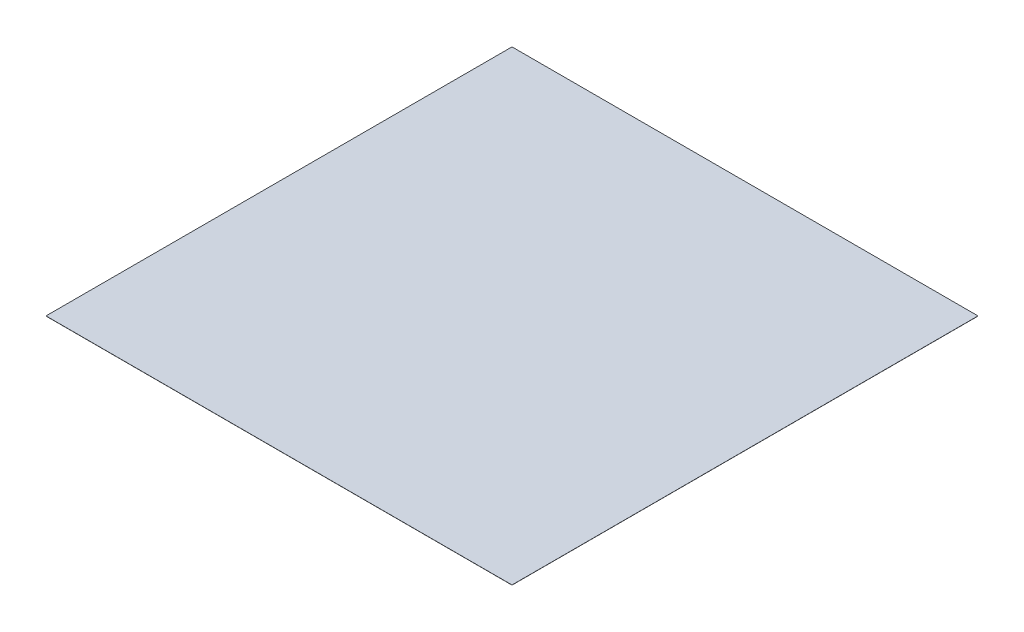
SolidWorks part; units mm, degrees
ref_plane "Front Plane" through (0, 0, 0) normal (0, 0, 1) x (1, 0, 0)
ref_plane "Top Plane" through (0, 0, 0) normal (0, 1, 0) x (1, 0, 0)
ref_plane "Right Plane" through (0, 0, 0) normal (1, 0, 0) x (0, 0, -1)
sketch "Sketch1" plane through (0, 0, 0) normal (0, 1, 0) x (1, 0, 0)
  line L1 (-1423.3391, 980.5341) -> (1576.6609, 980.5341)
  line L2 (-1423.3391, 980.5341) -> (-1423.3391, -2019.4659)
  line L3 (-1423.3391, -2019.4659) -> (1576.6609, -2019.4659)
  line L4 (1576.6609, 980.5341) -> (1576.6609, -2019.4659)
  dimension "D1" = 3000
  dimension "D2" = 3000
extrude "Boss-Extrude1" add sketch "Sketch1" along normal blind 1
